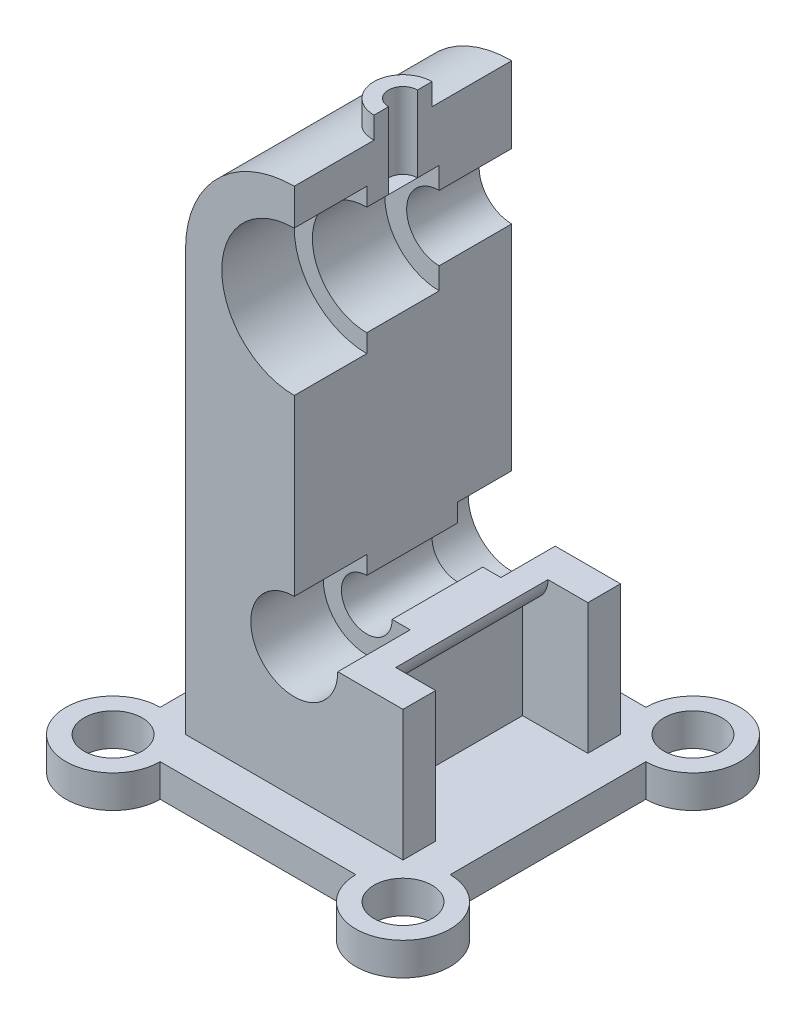
SolidWorks part; units mm, degrees
ref_plane "Ön Düzlem" through (0, 0, 0) normal (0, 0, 1) x (1, 0, 0)
ref_plane "Üst Düzlem" through (0, 0, 0) normal (0, 1, 0) x (1, 0, 0)
ref_plane "Sağ Düzlem" through (0, 0, 0) normal (1, 0, 0) x (0, 0, -1)
sketch "Çizim1" plane through (0, 0, 0) normal (1, 0, 0) x (0, 0, -1)
  line L1 (0, 0) -> (-60, 0)
  line L2 (0, 0) -> (0, 116)
  line L3 (0, 116) -> (-60, 116)
  line L4 (-60, 0) -> (-60, 116)
  dimension "D1" = 60
  dimension "D2" = 116
extrude "Yükseklik-Ekstrüzyon1" add sketch "Çizim1" along normal blind 60
sketch "Çizim2" plane through (0, 0, 0) normal (0, 1, 0) x (1, 0, 0)
  line L1 (-10, -83) -> (70, -83)
  line L3 (3, -70) -> (57, -70)
  line L7 (-23, -70) -> (-23, 10)
  line L8 (-10, 23) -> (70, 23)
  line L9 (83, 10) -> (83, -70)
  line L10 (60, -60) -> (0, -60) construction
  line L11 (70, -57) -> (70, -3)
  line L13 (60, 0) -> (0, 0) construction
  line L14 (57, 10) -> (3, 10)
  line L15 (-10, -3) -> (-10, -57)
  line L16 (0, 0) -> (0, -60) construction
  line L17 (60, 0) -> (60, -60) construction
  arc A0 (-10, -57) -> (3, -70) centre (-10, -70) ccw
  circle A1 centre (-10, -70) radius 8
  arc A2 (57, -70) -> (70, -57) centre (70, -70) ccw
  circle A3 centre (70, -70) radius 8
  arc A4 (70, -3) -> (57, 10) centre (70, 10) ccw
  circle A5 centre (70, 10) radius 8
  arc A6 (3, 10) -> (-10, -3) centre (-10, 10) ccw
  circle A7 centre (-10, 10) radius 8
  dimension "D7" = 26
  dimension "D8" = 16
  dimension "D9" = 26
  dimension "D10" = 16
  dimension "D11" = 26
  dimension "D12" = 16
  dimension "D13" = 26
  dimension "D14" = 16
  dimension "D20" = 10
  dimension "D21" = 13
  dimension "D1" = 80
  dimension "D2" = 80
  dimension "D3" = 80
  dimension "D4" = 80
  dimension "D5" = 10
  dimension "D6" = 10
  dimension "D15" = 80
  dimension "D16" = 10
  dimension "D17" = 10
  dimension "D18" = 10
  dimension "D19" = 13
extrude "Yükseklik-Ekstrüzyon2" add sketch "Çizim2" against normal blind 9 contours L14 A6 L15 A0 L3 A2 L11 A4 A7 A1 A3 A5
sketch "Çizim3" plane through (0, 0, 0) normal (0, 0, 1) x (1, 0, 0)
  line L0 (0, 116) -> (30, 116)
  line L2 (60, 116) -> (0, 116) construction
  circle A0 centre (30, 116) radius 30
  circle A1 centre (30, 116) radius 20
  dimension "D2" = 40
  dimension "D3" = 60
  dimension "D1" = 30
extrude "Yükseklik-Ekstrüzyon3" add sketch "Çizim3" along normal blind 60
sketch "Çizim4" plane through (0, 0, 60) normal (0, 0, 1) x (1, 0, 0)
  circle A0 centre (30, 116) radius 20
  dimension "D1" = 40
extrude "Kes-Ekstrüzyon1" cut sketch "Çizim4" against normal blind 20
sketch "Çizim5" plane through (0, 0, 40) normal (0, 0, 1) x (1, 0, 0)
  circle A0 centre (30, 116) radius 15
  dimension "D1" = 30
extrude "Kes-Ekstrüzyon2" cut sketch "Çizim5" against normal blind 20
sketch "Çizim6" plane through (0, 0, 20) normal (0, 0, 1) x (1, 0, 0)
  circle A0 centre (30, 116) radius 9
  dimension "D1" = 18
extrude "Kes-Ekstrüzyon3" cut sketch "Çizim6" against normal blind 20
sketch "Çizim7" plane through (0, 0, 60) normal (0, 0, 1) x (1, 0, 0)
  line L0 (0, 0) -> (0, 36)
  line L1 (0, 116) -> (0, 0) construction
  line L2 (0, 36) -> (18, 36)
  line L3 (60, 116) -> (60, 0) construction
  line L4 (42, 36) -> (60, 36)
  circle A0 centre (30, 36) radius 12
  dimension "D2" = 24
  dimension "D1" = 36
  dimension "D3" = 18
  dimension "D4" = 18
extrude "Kes-Ekstrüzyon4" cut sketch "Çizim7" against normal blind 20 contours A0
sketch "Çizim8" plane through (0, 0, 40) normal (0, 0, 1) x (1, 0, 0)
  circle A0 centre (30, 36) radius 7
  dimension "D1" = 14
extrude "Kes-Ekstrüzyon5" cut sketch "Çizim8" against normal blind 25
sketch "Çizim9" plane through (0, 0, 15) normal (0, 0, 1) x (1, 0, 0)
  circle A0 centre (30, 36) radius 12
  dimension "D1" = 24
extrude "Kes-Ekstrüzyon6" cut sketch "Çizim9" against normal blind 15
sketch "Çizim10" plane through (60, 0, 0) normal (1, 0, 0) x (0, 0, -1)
  line L0 (-51, 0) -> (-51, 36)
  line L1 (-60, 0) -> (0, 0) construction
  line L2 (-60, 0) -> (-60, 36)
  line L3 (-60, 116) -> (-60, 0) construction
  line L4 (0, 0) -> (0, 36)
  line L5 (0, 0) -> (0, 116) construction
  line L6 (-9, 0) -> (-9, 36)
  line L7 (-60, 36) -> (-51, 36)
  line L8 (-9, 36) -> (0, 36)
  line L9 (-51, 36) -> (-9, 36)
  line L10 (-60, 36) -> (-60, 116)
  line L11 (0, 36) -> (0, 116)
  line L12 (-60, 116) -> (0, 116)
  line M5 (0, 0) -> (0, 116)
  line M6 (0, 116) -> (-60, 116)
  line M7 (-60, 116) -> (-60, 0)
  dimension "D1" = 9
  dimension "D2" = 9
  dimension "D3" = 36
  dimension "D4" = 36
  dimension "D5" = 36
  dimension "D6" = 36
  dimension "D7" = 80
  dimension "D8" = 80
extrude "Kes-Ekstrüzyon8" cut sketch "Çizim10" against normal blind 30 contours L7 L9 L8 M5 M6 M7
ref_plane "Düzlem1" through (30, 0, 0) normal (1, 0, 0) x (0, 0, -1)
sketch "Çizim13" plane through (30, 0, 0) normal (1, 0, 0) x (0, 0, -1)
  line L0 (-60, 146) -> (-60, 116)
  line L1 (-60, 116) -> (0, 116)
  line L2 (0, 116) -> (0, 146)
  line L3 (0, 146) -> (-60, 146)
extrude "Kes-Ekstrüzyon9" cut sketch "Çizim13" along normal blind 30
ref_plane "Düzlem2" through (0, 146, 0) normal (0, 1, 0) x (1, 0, 0)
sketch "Çizim14" plane through (0, 146, 0) normal (0, 1, 0) x (1, 0, 0)
  line L1 (30, 0) -> (30, -60) construction
  circle A1 centre (30, -30) radius 4
  circle A2 centre (30, -30) radius 8
  dimension "D1" = 8
  dimension "D2" = 16
extrude "Yükseklik-Ekstrüzyon5" add sketch "Çizim14" against normal blind 15 and the other way blind 6
ref_plane "Düzlem4" through (0, 0, 46) normal (0, 0, 1) x (1, 0, 0)
sketch "Çizim16" plane through (0, 0, 46) normal (0, 0, 1) x (1, 0, 0)
  line L0 (30, 152) -> (30, 131)
  line L1 (38, 152) -> (22, 152) construction
  line L2 (30, 152) -> (38, 152)
  line L3 (38, 152) -> (38, 131)
  line L4 (38, 131) -> (30, 131)
extrude "Kes-Ekstrüzyon10" cut sketch "Çizim16" against normal blind 57
ref_plane "Düzlem5" through (0, 146, 0) normal (0, 1, 0) x (1, 0, 0)
sketch "Çizim17" plane through (0, 146, 0) normal (0, 1, 0) x (1, 0, 0)
  line L0 (30, -26) -> (30, -34) construction
  line L1 (30, -40) -> (30, -15) construction
  line L2 (30, -26) -> (30, -34)
  arc A0 (30, -34) -> (30, -26) centre (30, -30) cw
  dimension "D1" = 4
extrude "Kes-Ekstrüzyon12" cut sketch "Çizim17" against normal blind 15
sketch "Çizim18" plane through (60, 0, 0) normal (1, 0, 0) x (0, 0, -1)
  line L0 (-60, 0) -> (-60, 36)
  line L1 (-60, 36) -> (-51, 36)
  line L2 (-60, 36) -> (-40, 36) construction
  line L3 (-51, 36) -> (-51, 0)
  line L4 (-57, 0) -> (-3, 0) construction
  line L5 (-60, 0) -> (-51, 0)
  line L6 (0, 36) -> (0, 0)
  line L7 (0, 36) -> (-9, 36)
  line L8 (-15, 36) -> (0, 36) construction
  line L9 (-9, 36) -> (-9, 0)
  line L10 (-60, 0) -> (0, 0) construction
  line L11 (-9, 0) -> (0, 0)
  line L12 (-51, 36) -> (-9, 36)
  line L13 (-51, 0) -> (-9, 0)
  line M3 (0, 36) -> (-60, 36)
  line M5 (-60, 0) -> (0, 0)
  dimension "D1" = 9
  dimension "D2" = 9
extrude "Kes-Ekstrüzyon13" cut sketch "Çizim18" against normal blind 18 contours L9 L3 M3 M5
ref_plane "Düzlem6" through (0, 0, 60) normal (0, 0, 1) x (1, 0, 0)
ref_plane "Düzlem7" through (0, 0, 60) normal (0, 0, 1) x (1, 0, 0)
sketch "Çizim21" plane through (0, 0, 51) normal (0, 0, -1) x (-1, 0, 0)
  line L1 (-42, 36) -> (-42, 29)
  line L3 (-42, 36) -> (-42, 0) construction
  line L4 (-49, 36) -> (-42, 36)
  line L5 (-42, 36) -> (-60, 36) construction
  line L6 (-42, 36) -> (-42, 29)
  arc A1 (-49, 36) -> (-42, 29) centre (-42, 36) ccw
  line M8 (-42, 0) -> (-42, 36)
  line M9 (-42, 36) -> (-60, 36)
  dimension "D1" = 7
  dimension "D2" = 7
extrude "Yükseklik-Ekstrüzyon7" add sketch "Çizim21" along normal blind 42 contours A1 M9 M8
